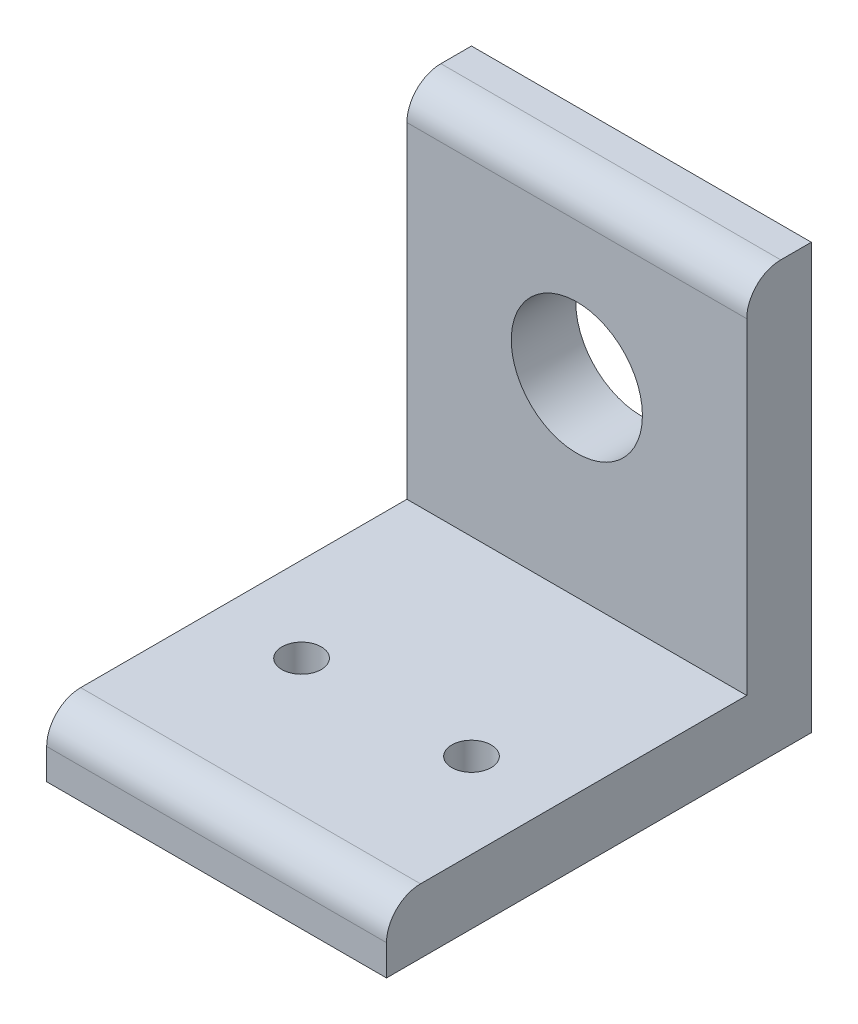
SolidWorks part; units mm, degrees
material "1060 Alloy"
ref_plane "Front Plane" through (0, 0, 0) normal (0, 0, 1) x (1, 0, 0)
ref_plane "Top Plane" through (0, 0, 0) normal (0, 1, 0) x (1, 0, 0)
ref_plane "Right Plane" through (0, 0, 0) normal (1, 0, 0) x (0, 0, -1)
sketch "Sketch2" plane through (0, 0, 0) normal (1, 0, 0) x (0, 0, -1)
  line L0 (0, 0) -> (31.75, 0)
  line L1 (31.75, 0) -> (31.75, 31.75)
  line L2 (31.75, 31.75) -> (26.924, 31.75)
  line L3 (26.924, 31.75) -> (26.924, 4.826)
  line L4 (26.924, 4.826) -> (0, 4.826)
  line L5 (0, 4.826) -> (0, 0)
  dimension "D1" = 31.75
  dimension "D2" = 31.75
  dimension "D3" = 4.826
  dimension "D4" = 4.826
extrude "Boss-Extrude1" add sketch "Sketch2" against normal blind 50.8
sketch "Sketch3" plane through (0, 0, -26.924) normal (0, 0, 1) x (1, 0, 0)
  line L0 (-50.8, 0) -> (0, 0) construction
  line L1 (-50.8, 31.75) -> (-50.8, 4.826) construction
  circle A0 centre (-38.1, 19.05) radius 4.9022
  circle A1 centre (-12.7, 19.05) radius 4.9022
  dimension "D1" = 9.8044
  dimension "D2" = 19.05
  dimension "D3" = 12.7
  dimension "D4" = 38.1
extrude "Cut-Extrude1" cut sketch "Sketch3" against normal blind 50.8
sketch "Sketch4" plane through (0, 4.826, 0) normal (0, 1, 0) x (1, 0, 0)
  line L0 (-50.8, 31.75) -> (0, 31.75) construction
  line L1 (-50.8, 26.924) -> (-50.8, 0) construction
  circle A0 centre (-44.45, 12.7) radius 1.4732
  circle A1 centre (-31.75, 12.7) radius 1.4732
  dimension "D1" = 2.9464
  dimension "D2" = 19.05
  dimension "D3" = 6.35
  dimension "D4" = 19.05
extrude "Cut-Extrude2" cut sketch "Sketch4" against normal blind 50.8
fillet "Fillet1" radius 2.54 2 edges at (-25.4, 4.826, 0) (-25.4, 31.75, -26.924)
sketch "Sketch5" plane through (0, 0, -26.924) normal (0, 0, 1) x (1, 0, 0)
  line L0 (-25.4, 31.75) -> (-25.4, 0)
  line L1 (-50.8, 31.75) -> (0, 31.75) construction
  line L2 (-50.8, 0) -> (0, 0) construction
  line L5 (-25.4, 31.75) -> (0, 31.75)
  line L6 (0, 31.75) -> (0, 0)
  line L7 (0, 0) -> (-25.4, 0)
  circle A0 centre (-38.1, 19.05) radius 4.9022 construction
  point P10 (-38.1, 14.1478)
extrude "Cut-Extrude3" cut sketch "Sketch5" against normal through all both and the other way through all
